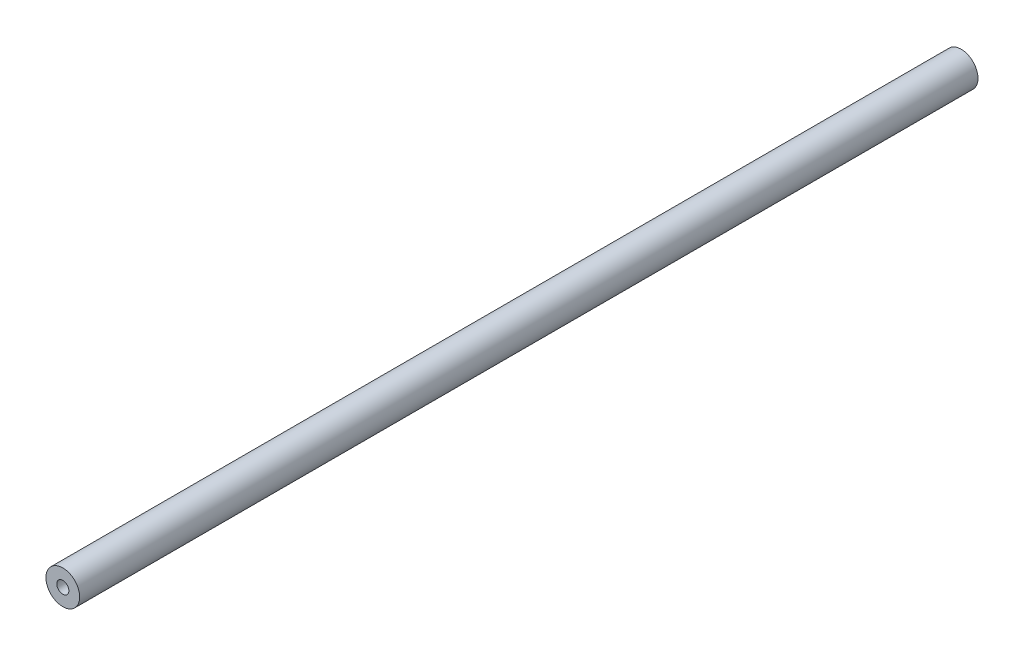
SolidWorks part; units mm, degrees
material "Alloy Steel"
ref_plane "Front Plane" through (0, 0, 0) normal (0, 0, 1) x (1, 0, 0)
ref_plane "Top Plane" through (0, 0, 0) normal (0, 1, 0) x (1, 0, 0)
ref_plane "Right Plane" through (0, 0, 0) normal (1, 0, 0) x (0, 0, -1)
sketch "Sketch1" plane through (0, 0, 0) normal (0, 0, 1) x (1, 0, 0)
  circle A0 centre (0, 0) radius 6
  circle A1 centre (0, 0) radius 2.5 construction
  dimension "D1" = 12
  dimension "D2" = 5
extrude "Boss-Extrude1" add sketch "Sketch1" along normal blind 320
sketch "Sketch2" plane through (0, 0, 320) normal (0, 0, 1) x (1, 0, 0)
  circle A0 centre (0, 0) radius 2.15
  dimension "D1" = 4.3
extrude "Cut-Extrude1" cut sketch "Sketch2" against normal blind 20
sketch "Sketch3" plane through (0, 0, 0) normal (0, 0, -1) x (-1, 0, 0)
  circle A0 centre (0, 0) radius 2.15
  dimension "D1" = 4.3
extrude "Cut-Extrude2" cut sketch "Sketch3" against normal blind 20
